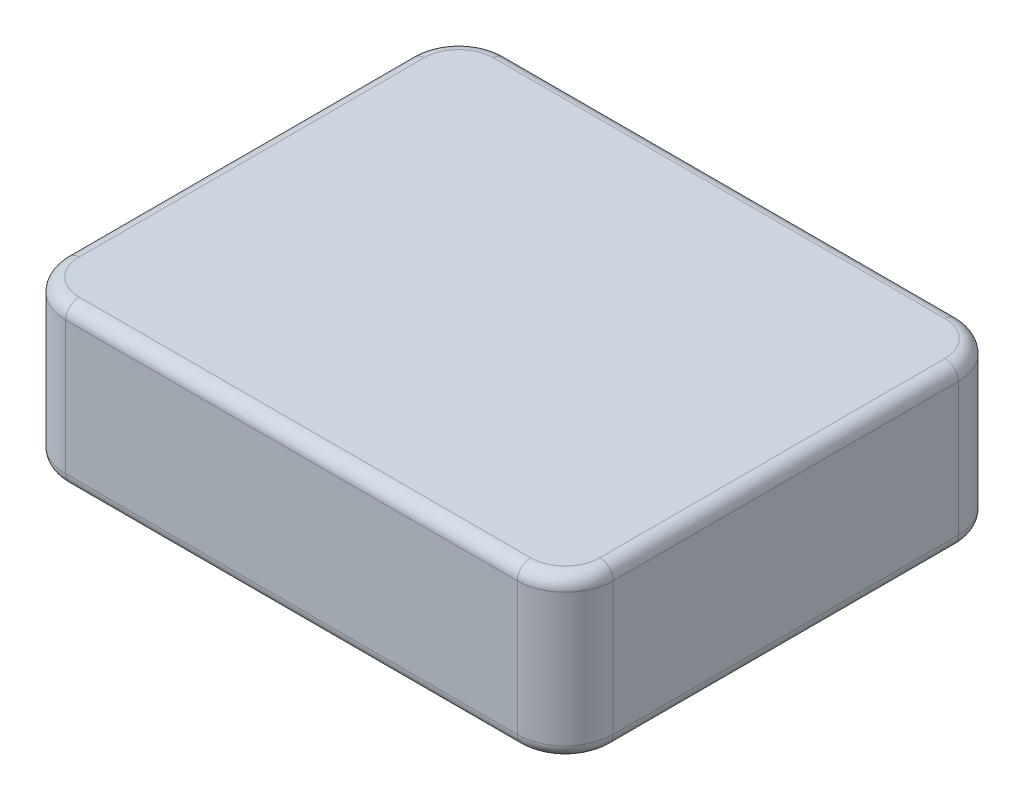
SolidWorks part; units mm, degrees
ref_plane "Front Plane" through (0, 0, 0) normal (0, 0, 1) x (1, 0, 0)
ref_plane "Top Plane" through (0, 0, 0) normal (0, 1, 0) x (1, 0, 0)
ref_plane "Right Plane" through (0, 0, 0) normal (1, 0, 0) x (0, 0, -1)
sketch "Sketch1" plane through (0, 0, 0) normal (0, 1, 0) x (1, 0, 0)
  line L1 (-16.965, -16.565) -> (16.965, -16.565)
  line L2 (-20.565, -12.965) -> (-20.565, 12.965)
  line L3 (-16.965, 16.565) -> (16.965, 16.565)
  line L4 (20.565, -12.965) -> (20.565, 12.965)
  line L5 (-20.565, -16.565) -> (20.565, 16.565) construction
  line L6 (-20.565, 16.565) -> (20.565, -16.565) construction
  arc A0 (16.965, -16.565) -> (20.565, -12.965) centre (16.965, -12.965) ccw
  arc A1 (16.965, 16.565) -> (20.565, 12.965) centre (16.965, 12.965) cw
  arc A2 (-16.965, -16.565) -> (-20.565, -12.965) centre (-16.965, -12.965) cw
  arc A3 (-20.565, 12.965) -> (-16.965, 16.565) centre (-16.965, 12.965) cw
  point P0 (0, 0)
  dimension "D3" = 3.6
  dimension "D1" = 33.13
  dimension "D2" = 41.13
extrude "Boss-Extrude1" add sketch "Sketch1" along normal mid plane 12
fillet "Fillet1" radius 1 16 edges at (20.565, -6, 0) (19.5106, -6, -15.5106) (0, -6, -16.565) (-19.5106, -6, -15.5106) (-20.565, -6, 0) (-19.5106, -6, 15.5106) (0, -6, 16.565) (19.5106, -6, 15.5106) (0, 6, 16.565) (-19.5106, 6, 15.5106) (-20.565, 6, 0) (-19.5106, 6, -15.5106) (0, 6, -16.565) (19.5106, 6, -15.5106) (20.565, 6, 0) (19.5106, 6, 15.5106)
